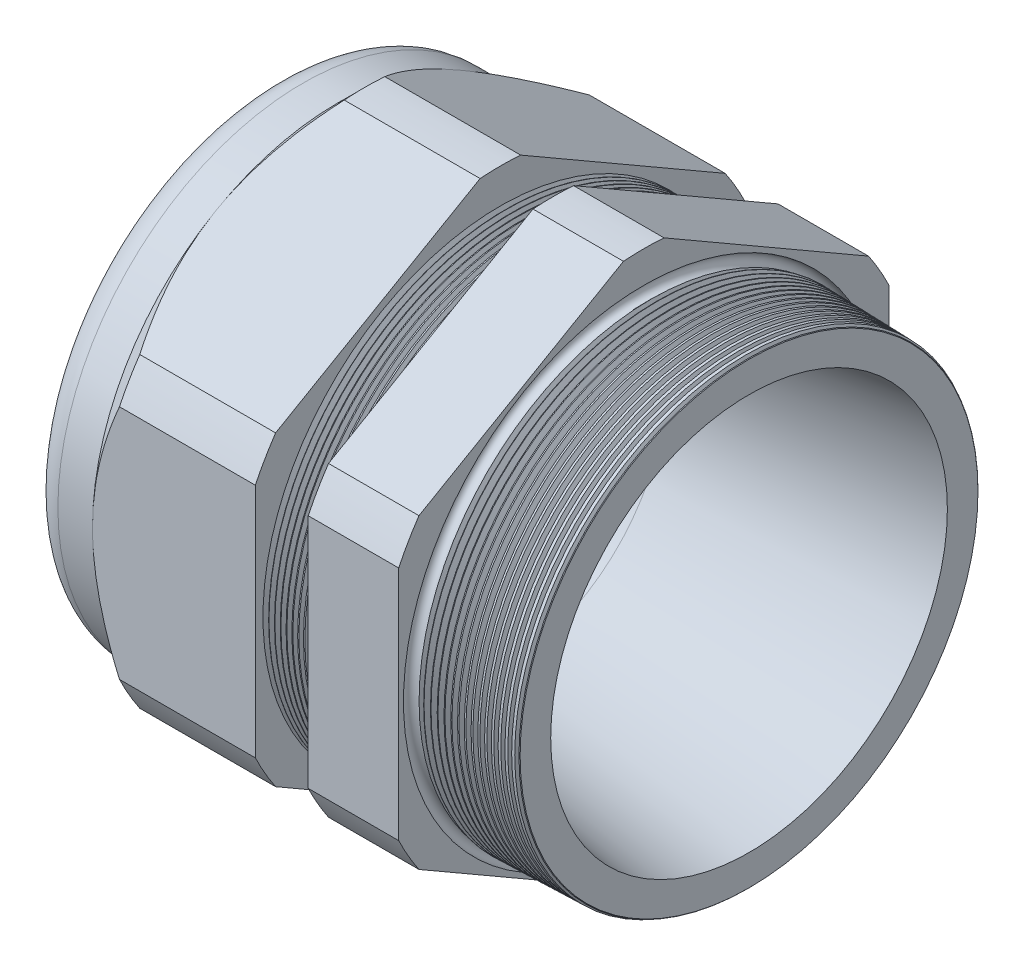
SolidWorks part; units mm, degrees
ref_plane "Front Plane" through (0, 0, 0) normal (0, 0, 1) x (1, 0, 0)
ref_plane "Top Plane" through (0, 0, 0) normal (0, 1, 0) x (1, 0, 0)
ref_plane "Right Plane" through (0, 0, 0) normal (1, 0, 0) x (0, 0, -1)
sketch "Sketch10" plane through (0, 0, 0) normal (0, 0, 1) x (1, 0, 0)
  line L0 (0, 0) -> (-115.3565, 0) construction
  line L1 (-56.896, 21.971) -> (-26.8936, 21.971)
  line L2 (6.096, 26.3141) -> (6.096, 30.6321)
  line L3 (-7.874, 30.998) -> (6.096, 30.6321)
  line L4 (-7.874, 65.024) -> (-7.874, 30.998)
  line L5 (-7.874, 65.024) -> (-19.874, 65.024)
  line L6 (-19.874, 65.024) -> (-19.874, 31.3122)
  line L7 (-26.8936, 31.496) -> (-19.874, 31.3122)
  line L8 (-26.8936, 31.496) -> (-26.8936, 65.024)
  line L9 (-26.8936, 65.024) -> (-48.496, 65.024)
  line L10 (-48.496, 65.024) -> (-48.496, 32.512)
  line L11 (-48.496, 32.512) -> (-56.896, 32.512)
  line L12 (-56.896, 32.512) -> (-56.896, 21.971)
  line L13 (-26.8936, 21.971) -> (6.096, 26.3141)
  dimension "D1" = 62.992
  dimension "D2" = 43.942
  dimension "D3" = 1.5
  dimension "D4" = 4.318
  dimension "A" = 62.992
  dimension "D6" = 65.024
  dimension "D8" = 130.048
  dimension "D9" = 8.4
  dimension "D10" = 21.6024
  dimension "D11" = 12
  dimension "D" = 13.97
revolve "Revolve2" add sketch "Sketch10" angle 360 about L0
sketch "Sketch12" plane through (-48.496, 0, 0) normal (-1, 0, 0) x (0, 0, 1)
  line L1 (-2.6912, 35.9878) -> (-29.8208, 20.3246)
  line L2 (-32.512, 15.6632) -> (-32.512, -15.6632)
  line L3 (-29.8208, -20.3246) -> (-2.6912, -35.9878)
  line L4 (2.6912, -35.9878) -> (29.8208, -20.3246)
  line L5 (32.512, -15.6632) -> (32.512, 15.6632)
  line L6 (29.8208, 20.3246) -> (2.6912, 35.9878)
  circle A0 centre (0, 0) radius 32.512 construction
  arc A1 (2.6912, 35.9878) -> (-2.6912, 35.9878) centre (0, 0) ccw
  arc A2 (-29.8208, 20.3246) -> (-32.512, 15.6632) centre (0, 0) ccw
  arc A3 (-32.512, -15.6632) -> (-29.8208, -20.3246) centre (0, 0) ccw
  arc A4 (-2.6912, -35.9878) -> (2.6912, -35.9878) centre (0, 0) ccw
  arc A5 (29.8208, -20.3246) -> (32.512, -15.6632) centre (0, 0) ccw
  arc A6 (32.512, 15.6632) -> (29.8208, 20.3246) centre (0, 0) ccw
  dimension "D2" = 72.1766
  dimension "D1" = 65.024
extrude "Cut-Extrude2" cut sketch "Sketch12" against normal through all flip side to cut
fillet "Fillet4" radius 3.81 1 edges at (-56.896, 0, -32.512)
sketch "Sketch19" plane through (-48.496, 0, 0) normal (-1, 0, 0) x (0, 0, 1)
  line L0 (32.512, 0) -> (32.512, 15.6632) construction
  circle A0 centre (0, 0) radius 32.512
extrude "Cut-Extrude3" cut sketch "Sketch19" against normal blind 3.998 draft 45 flip side to cut
chamfer "Chamfer1" distance 0.254 angle 45 1 edges at (6.096, 0, -30.6321)
sketch "Sketch21" plane through (-56.896, 0, 0) normal (-1, 0, 0) x (0, 0, 1)
  circle A0 centre (0, 0) radius 21.971
  circle A2 centre (0, 0) radius 21.971 construction
extrude "plug" add sketch "Sketch21" against normal blind 12.7 separate body
sketch "Sketch22" plane through (-56.896, 0, 0) normal (-1, 0, 0) x (0, 0, 1)
  circle A0 centre (0, 0) radius 21.717
  circle A1 centre (0, 0) radius 21.971 construction
  dimension "D1" = 0.254
extrude "Cut-Extrude4" cut sketch "Sketch22" against normal blind 0.508
sketch "Sketch27" plane through (-56.388, 0, 0) normal (-1, 0, 0) x (0, 0, 1)
  line L0 (-4.3624, 0) -> (4.3624, 0) construction
  circle A0 centre (-15.7241, 0) radius 5.969
  circle A1 centre (0, 0) radius 21.717 construction
  dimension "D1" = 0.0239
  dimension "holedia" = 11.938
extrude "plugholes" cut sketch "Sketch27" against normal through all
pattern_circular "CirPattern1" count 6 over 360 about axis through (0, 0, 0) along (1, 0, 0) of "plugholes"
sketch "Sketch28" [suppressed] plane through (-38.354, 0, 0) normal (-1, 0, 0) x (0, 0, 1)
  circle A0 centre (0, 0) radius 1.905
  dimension "midholedia" = 11.938
extrude "midhole" [suppressed] cut sketch "Sketch28" against normal through all
sketch "Sketch29" plane through (0, 0, 0) normal (0, 0, 1) x (1, 0, 0)
  line L0 (-26.8936, 31.496) -> (-26.1606, 31.4768)
  line L1 (-19.874, 31.3122) -> (-26.8936, 31.496) construction
  line L2 (-26.1606, 31.4768) -> (-26.5437, 30.8516)
  line L3 (-26.5437, 30.8516) -> (-26.8936, 31.496)
  dimension "D1" = 60
  dimension "D2" = 60
  dimension "D3" = 0.635
revolve "Cut-Revolve1" cut sketch "Sketch29" angle 360 about axis through (0, 0, 0) along (-1, 0, 0)
pattern_linear "LPattern1" count 9 spacing 0.762 along (1, 0, 0) of "Cut-Revolve1"
sketch "Sketch30" plane through (0, 0, 0) normal (0, 0, 1) x (1, 0, 0)
  line L0 (-7.874, 30.998) -> (-6.9944, 30.9749)
  line L1 (-7.874, 35.9878) -> (-7.874, 20.3246) construction
  line L2 (5.8421, 30.6388) -> (-7.874, 30.998) construction
  line L3 (-6.9944, 30.9749) -> (-7.4542, 30.2247)
  line L4 (-7.4542, 30.2247) -> (-7.874, 30.998)
  dimension "D1" = 60
  dimension "D2" = 60
  dimension "D3" = 0.762
revolve "Cut-Revolve2" cut sketch "Sketch30" angle 360 about axis through (0, 0, 0) along (-1, 0, 0)
pattern_linear "LPattern2" count 16 spacing 0.889 along (1, 0, 0) of "Cut-Revolve2"
sketch "Sketch31" [suppressed] plane through (-38.354, 0, 0) normal (-1, 0, 0) x (0, 0, 1)
  line L0 (-1.905, 1.905) -> (1.905, 1.905)
  line L1 (-1.905, -1.905) -> (1.905, -1.905)
  circle A0 centre (0, 0) radius 1.905 construction
  arc A1 (-1.905, 1.905) -> (-1.905, -1.905) centre (-1.905, 0) ccw
  arc A2 (1.905, 1.905) -> (1.905, -1.905) centre (1.905, 0) cw
extrude "Cut-Extrude5" [suppressed] cut sketch "Sketch31" against normal through all
sketch "Sketch32" plane through (0, 0, 0) normal (0, 0, 1) x (1, 0, 0)
  line L0 (-7.874, 35.9878) -> (-7.874, 20.3246) construction
  circle A0 centre (-7.747, 30.998) radius 0.889
  dimension "D2" = 1.778
  dimension "D1" = 0.127
revolve "Cut-Revolve3" cut sketch "Sketch32" angle 360 about axis through (0, 0, 0) along (-1, 0, 0)
